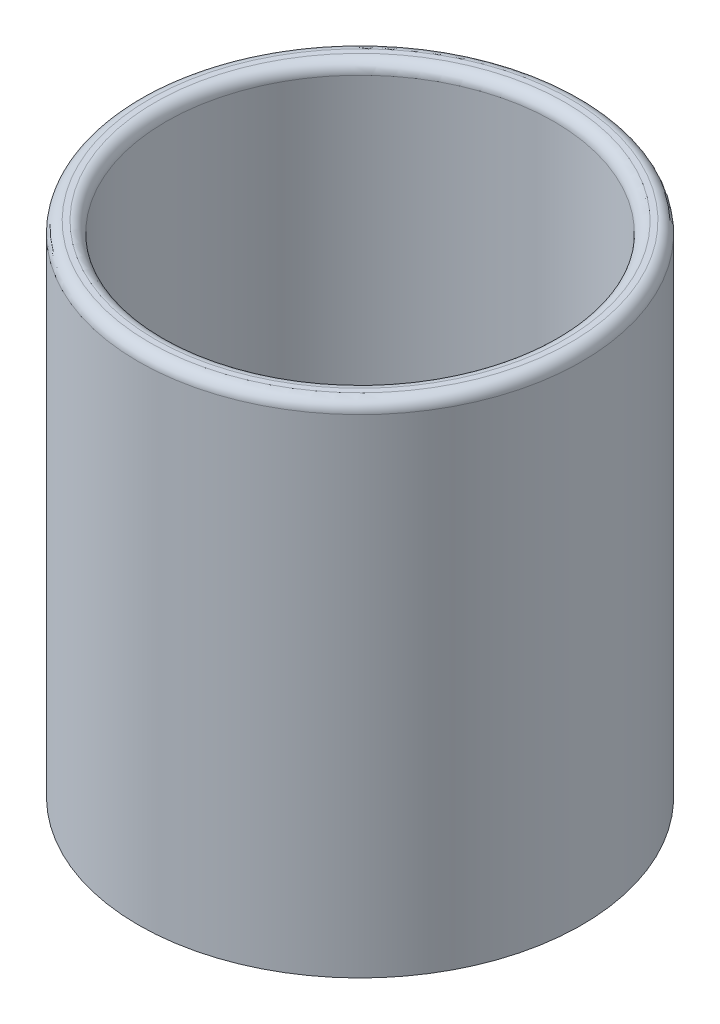
SolidWorks part; units mm, degrees
ref_plane "Front Plane" through (0, 0, 0) normal (0, 0, 1) x (1, 0, 0)
ref_plane "Top Plane" through (0, 0, 0) normal (0, 1, 0) x (1, 0, 0)
ref_plane "Right Plane" through (0, 0, 0) normal (1, 0, 0) x (0, 0, -1)
sketch "Sketch1" plane through (0, 0, 0) normal (0, 1, 0) x (1, 0, 0)
  circle A1 centre (0, 0) radius 40
  dimension "D1" = 80
extrude "Boss-Extrude1" add sketch "Sketch1" along normal blind 90
sketch "Sketch2" plane through (0, 90, 0) normal (0, 1, 0) x (1, 0, 0)
  circle A0 centre (0, 0) radius 35
  dimension "D1" = 70
extrude "Cut-Extrude1" cut sketch "Sketch2" against normal blind 85
fillet "Fillet1" radius 2 1 edges at (0, 90, 40)
fillet "Fillet2" radius 2 1 edges at (0, 90, 35)
fillet "Fillet4" radius 5 1 edges at (0, 5, 35)
